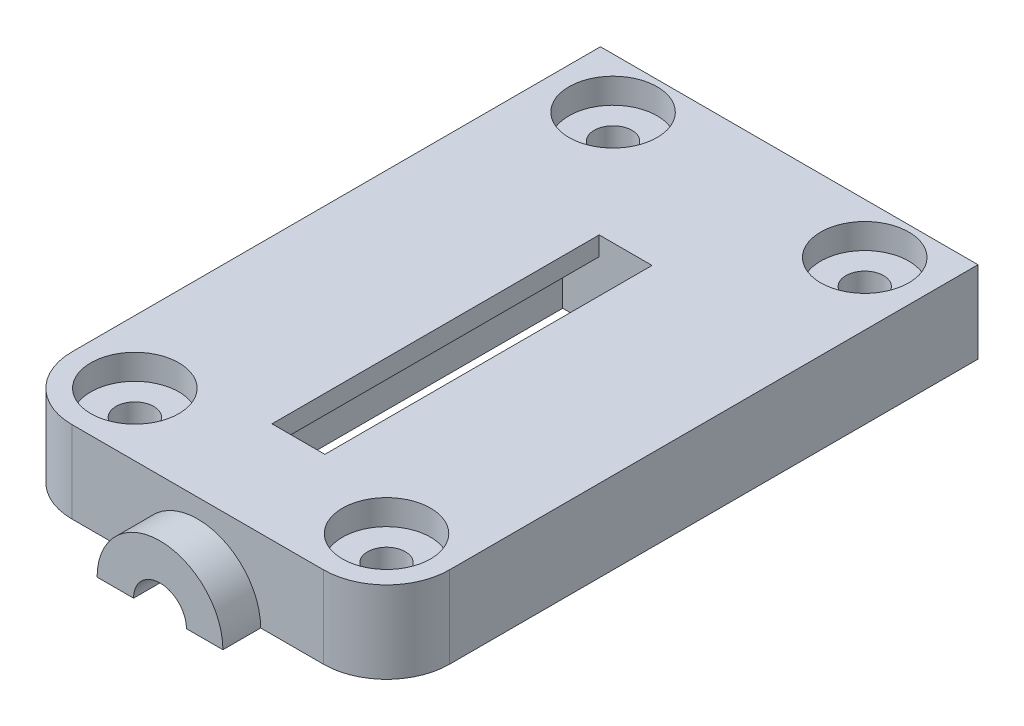
SolidWorks part; units mm, degrees
ref_plane "Front Plane" through (0, 0, 0) normal (0, 0, 1) x (1, 0, 0)
ref_plane "Top Plane" through (0, 0, 0) normal (0, 1, 0) x (1, 0, 0)
ref_plane "Right Plane" through (0, 0, 0) normal (1, 0, 0) x (0, 0, -1)
sketch "Sketch1" plane through (0, 0, 0) normal (0, 1, 0) x (1, 0, 0)
  line L1 (15, -23.5) -> (-15, -23.5)
  line L2 (15, -23.5) -> (15, 23.5)
  line L3 (15, 23.5) -> (-15, 23.5)
  line L4 (-15, -23.5) -> (-15, 23.5)
  line L5 (15, -23.5) -> (-15, 23.5) construction
  line L6 (15, 23.5) -> (-15, -23.5) construction
  point P0 (0, 0)
extrude "Boss-Extrude1" add sketch "Sketch1" along normal blind 6.5
sketch "Sketch2" plane through (0, 0, 23.5) normal (0, 0, 1) x (1, 0, 0)
  line L0 (-15, 0) -> (15, 0) construction
  line L1 (5, 0) -> (-5, 0)
  arc A0 (5, 0) -> (-5, 0) centre (0, 0) ccw
extrude "Boss-Extrude2" add sketch "Sketch2" along normal blind 3
sketch "Sketch3" plane through (0, 0, 26.5) normal (0, 0, 1) x (1, 0, 0)
  circle A0 centre (0, 0) radius 2.1
extrude "Cut-Extrude1" cut sketch "Sketch3" against normal blind 50
fillet "Fillet1" radius 5 2 edges at (-15, 3.25, 23.5) (15, 3.25, 23.5)
ref_plane "Plane1" through (0, 0, 20) normal (0, 0, 1) x (1, 0, 0)
sketch "Sketch4" plane through (0, 0, 20) normal (0, 0, 1) x (1, 0, 0)
  circle A0 centre (0, 0) radius 4.1
extrude "Cut-Extrude2" cut sketch "Sketch4" against normal blind 3.1
sketch "Sketch5" plane through (0, 0, 0) normal (0, -1, 0) x (1, 0, 0)
  line L2 (-5, 15.5) -> (5, 15.5)
  line L3 (-5, 15.5) -> (-5, -10.5)
  line L4 (-5, -10.5) -> (5, -10.5)
  line L5 (5, 15.5) -> (5, -10.5)
extrude "Cut-Extrude3" cut sketch "Sketch5" against normal blind 5
ref_plane "Plane2" through (0, 0, -12) normal (0, 0, 1) x (1, 0, 0)
sketch "Sketch9" plane through (0, 0, -12) normal (0, 0, 1) x (1, 0, 0)
  circle A0 centre (0, 0) radius 4.1
extrude "Cut-Extrude4" cut sketch "Sketch9" against normal blind 3.1
ref_plane "Plane3" through (0, 0, -16.6) normal (0, 0, 1) x (1, 0, 0)
sketch "Sketch10" plane through (0, 0, -16.6) normal (0, 0, 1) x (1, 0, 0)
  circle A0 centre (0, 0) radius 5
extrude "Cut-Extrude5" cut sketch "Sketch10" against normal blind 6
sketch "Sketch11" plane through (0, 0, 0) normal (0, -1, 0) x (1, 0, 0)
  circle A0 centre (10, 18.5) radius 1.5
  circle A1 centre (10, -19.5) radius 1.5
  circle A2 centre (-10, -19.5) radius 1.5
  circle A3 centre (-10, 18.5) radius 1.5
extrude "Cut-Extrude6" cut sketch "Sketch11" against normal through all
sketch "Sketch12" plane through (0, 6.5, 0) normal (0, 1, 0) x (1, 0, 0)
  circle A0 centre (-10, 19.5) radius 3.5
  circle A1 centre (10, 19.5) radius 3.5
  circle A2 centre (10, -18.5) radius 3.5
  circle A3 centre (-10, -18.5) radius 3.5
extrude "Cut-Extrude7" cut sketch "Sketch12" against normal blind 2
sketch "Sketch13" plane through (0, 5, 0) normal (0, -1, 0) x (1, 0, 0)
  line L0 (0, -10.5) -> (2.1, -10.5)
  line L1 (2.1, -10.5) -> (-2.1, -10.5) construction
  line L2 (-5, -10.5) -> (5, -10.5) construction
  line L3 (0, -10.5) -> (-2.1, -10.5)
  line L4 (2.1, -10.5) -> (2.1, 15.5)
  line L5 (5, 15.5) -> (2.1, 15.5) construction
  line L6 (2.1, 15.5) -> (-2.1, 15.5)
  line L7 (-2.1, 15.5) -> (-5, 15.5) construction
  line L8 (-2.1, 15.5) -> (-2.1, -10.5)
extrude "Cut-Extrude8" cut sketch "Sketch13" against normal through all
